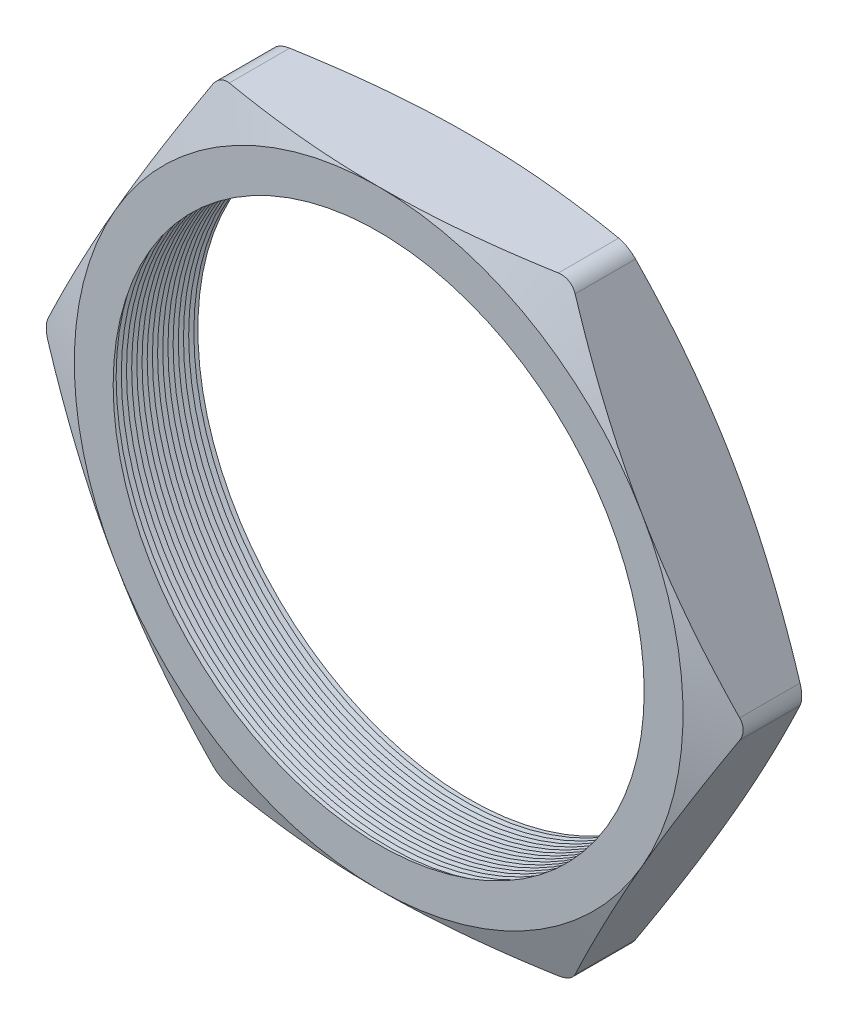
SolidWorks part; units mm, degrees
ref_plane "Front Plane" through (0, 0, 0) normal (0, 0, 1) x (1, 0, 0)
ref_plane "Top Plane" through (0, 0, 0) normal (0, 1, 0) x (1, 0, 0)
ref_plane "Right Plane" through (0, 0, 0) normal (1, 0, 0) x (0, 0, -1)
sketch "Sketch1" plane through (0, 0, 0) normal (0, 0, 1) x (1, 0, 0)
  line L1 (-13.7848, 0) -> (-6.8924, -11.938)
  line L2 (-6.8924, -11.938) -> (6.8924, -11.938)
  line L3 (6.8924, -11.938) -> (13.7848, 0)
  line L4 (13.7848, 0) -> (6.8924, 11.938)
  line L5 (6.8924, 11.938) -> (-6.8924, 11.938)
  line L6 (-6.8924, 11.938) -> (-13.7848, 0)
  circle A0 centre (0, 0) radius 11.938 construction
  circle A1 centre (0, 0) radius 10.414
  dimension "TS" = 20.828
  dimension "H" = 23.876
extrude "Extrude1" add sketch "Sketch1" along normal blind 3.556
fillet "Fillet1" radius 0.762 6 edges at (-6.8924, 11.938, 1.778) (-13.7848, 0, 1.778) (-6.8924, -11.938, 1.778) (6.8924, -11.938, 1.778) (13.7848, 0, 1.778) (6.8924, 11.938, 1.778)
sketch "Sketch2" plane through (0, 0, 3.556) normal (0, 0, 1) x (1, 0, 0)
  line L0 (6.4525, 11.938) -> (-6.4525, 11.938) construction
  circle A0 centre (0, 0) radius 11.938
extrude "Cut-Extrude1" cut sketch "Sketch2" against normal through all draft 70 flip side to cut
sketch "Sketch3" plane through (0, 0, 0) normal (0, 0, -1) x (-1, 0, 0)
  circle A0 centre (0, 0) radius 11.938
extrude "Cut-Extrude2" cut sketch "Sketch3" against normal through all draft 70 flip side to cut
sketch "Sketch4" plane through (0, 0, 0) normal (0, 1, 0) x (1, 0, 0)
  line L0 (-10.414, -3.556) -> (-10.414, -3.1161)
  line L2 (-10.414, -3.1161) -> (-10.795, -3.336)
  line L3 (-10.795, -3.336) -> (-10.414, -3.556)
  line L5 (-10.414, 0) -> (-10.414, -3.556) construction
  line L6 (-10.414, -3.556) -> (10.414, -3.556) construction
  dimension "D1" = 60
  dimension "D2" = 60
  dimension "D3" = 0.381
revolve "Cut-Revolve1" cut sketch "Sketch4" angle 360 about axis through (0, 0, 3.556) along (0, 0, -1)
pattern_linear "LPattern1" count 18 spacing 0.2032 along (0, 0, -1) of "Cut-Revolve1"
